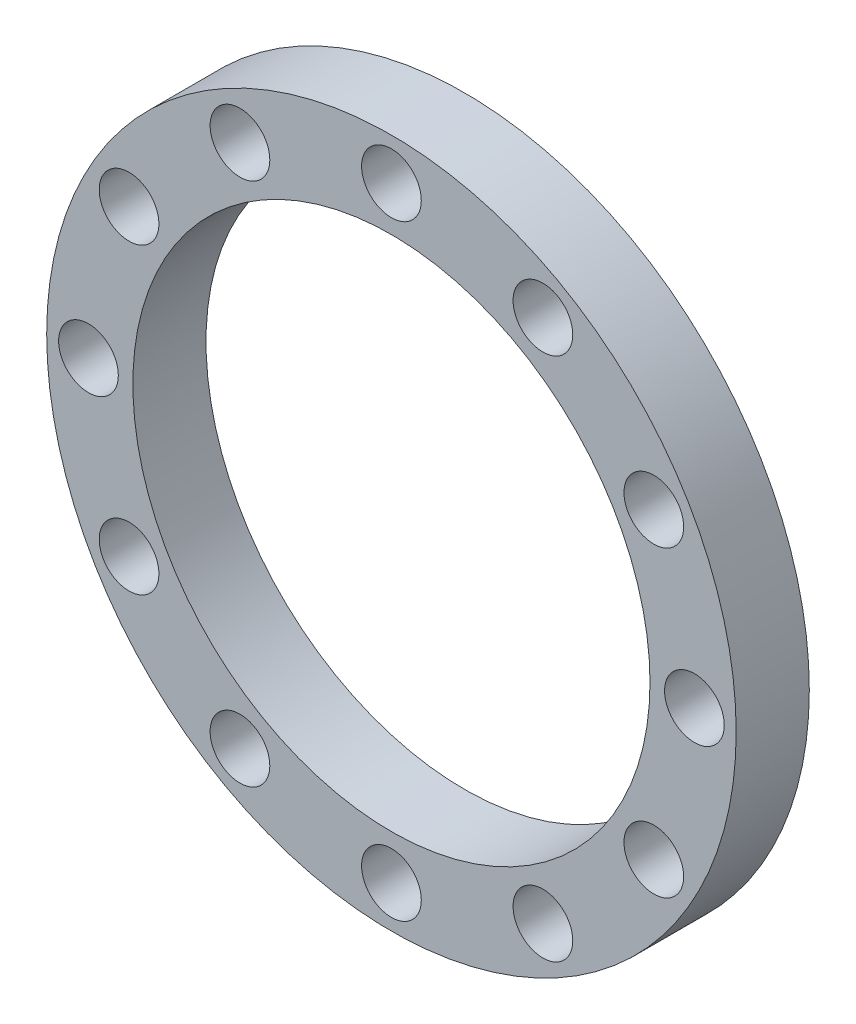
SolidWorks part; units mm, degrees
ref_plane "Front Plane" through (0, 0, 0) normal (0, 0, 1) x (1, 0, 0)
ref_plane "Top Plane" through (0, 0, 0) normal (0, 1, 0) x (1, 0, 0)
ref_plane "Right Plane" through (0, 0, 0) normal (1, 0, 0) x (0, 0, -1)
sketch "Sketch1" plane through (0, 0, 0) normal (0, 0, 1) x (1, 0, 0)
  circle A0 centre (0, 0) radius 330
  circle A1 centre (0, 0) radius 247.5
  dimension "D1" = 660
  dimension "D2" = 495
extrude "Boss-Extrude1" add sketch "Sketch1" along normal blind 70
sketch "Sketch2" plane through (0, 0, 0) normal (0, 0, 1) x (1, 0, 0)
  circle A0 centre (0, 0) radius 290
  circle A1 centre (0, 290) radius 28.575
  circle A2 centre (145, 251.1474) radius 28.575
  circle A3 centre (251.1474, 145) radius 28.575
  circle A4 centre (290, 0) radius 28.575
  circle A5 centre (251.1474, -145) radius 28.575
  circle A6 centre (145, -251.1474) radius 28.575
  circle A7 centre (0, -290) radius 28.575
  circle A8 centre (-145, -251.1474) radius 28.575
  circle A9 centre (-251.1474, -145) radius 28.575
  circle A10 centre (-290, 0) radius 28.575
  circle A11 centre (-251.1474, 145) radius 28.575
  circle A12 centre (-145, 251.1474) radius 28.575
  point P30 (0, 0)
  dimension "D1" = 580
  dimension "D2" = 57.15
  dimension "D3" = 12
extrude "Cut-Extrude1" cut sketch "Sketch2" along normal blind 131 contours A0 A4 | A0 A4 | A0 A6 | A0 A8 | A0 A8 | A5 | A7 | A9 | A10 | A11 | A12 | A1 | A2 | A3
equation "\"2.25inch\"=0.0379964"
